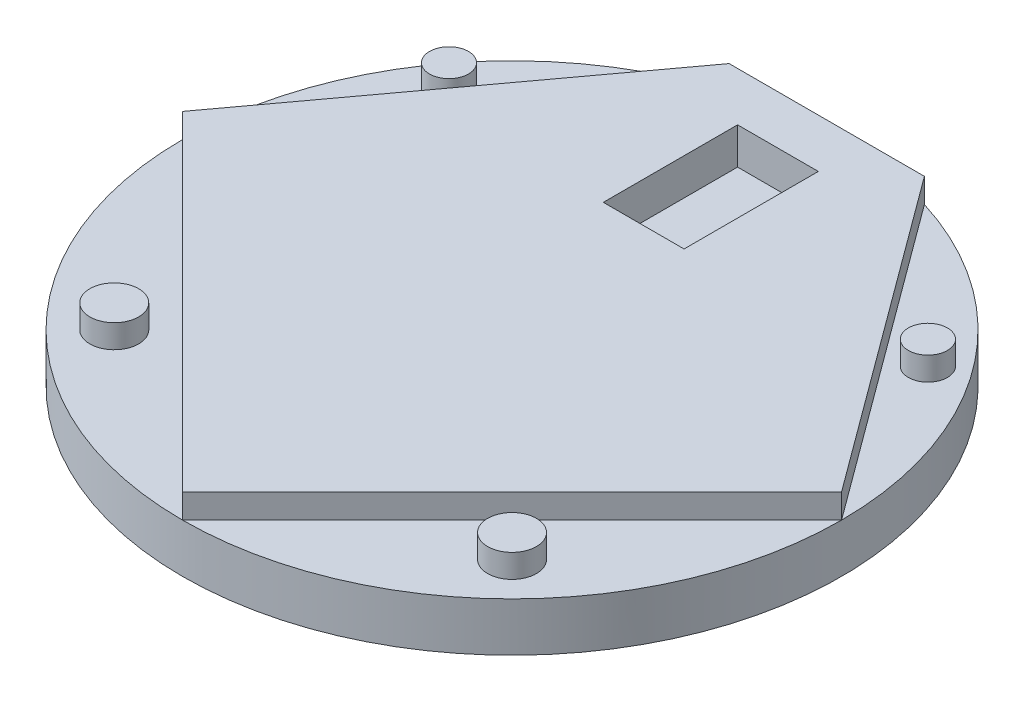
SolidWorks part; units mm, degrees
ref_plane "Front Plane" through (0, 0, 0) normal (0, 0, 1) x (1, 0, 0)
ref_plane "Top Plane" through (0, 0, 0) normal (0, 1, 0) x (1, 0, 0)
ref_plane "Right Plane" through (0, 0, 0) normal (1, 0, 0) x (0, 0, -1)
sketch "Sketch1" plane through (0, 0, 0) normal (0, 1, 0) x (1, 0, 0)
  circle A0 centre (0, 0) radius 85.725
extrude "Boss-Extrude1" add sketch "Sketch1" along normal blind 12.7
sketch "Sketch2" plane through (0, 12.7, 0) normal (0, 1, 0) x (1, 0, 0)
  line L0 (0, 0) -> (0, 85.725) construction
  line L1 (0, 0) -> (-85.725, 0) construction
  line L2 (-85.725, 0) -> (85.725, 0) construction
  line L3 (-25.4, 81.8756) -> (25.4, 81.8756)
  line L5 (-25.4, 81.8756) -> (-85.725, 0)
  line L6 (-85.725, 0) -> (0, -85.725)
  line L7 (0, -85.725) -> (85.725, 0)
  line L8 (85.725, 0) -> (25.4, 81.8756)
  circle A0 centre (0, 0) radius 85.725 construction
  dimension "D1" = 50.8
extrude "Boss-Extrude2" add sketch "Sketch2" along normal blind 6.35
sketch "Sketch3" plane through (0, 12.7, 0) normal (0, 1, 0) x (1, 0, 0)
  line L0 (-42.8625, -42.8625) -> (-60.6167, -60.6167) construction
  line L1 (-85.725, 0) -> (0, -85.725) construction
  line L2 (60.6167, -60.6167) -> (42.8625, -42.8625) construction
  line L3 (0, -85.725) -> (85.725, 0) construction
  line L4 (55.5625, 40.9378) -> (69.0152, 50.8496) construction
  line L5 (85.725, 0) -> (25.4, 81.8756) construction
  line L6 (-69.0152, 50.8496) -> (-55.5625, 40.9378) construction
  line L7 (-25.4, 81.8756) -> (-85.725, 0) construction
  circle A0 centre (-51.7396, -51.7396) radius 6.35
  arc A1 (-85.725, 0) -> (0, -85.725) centre (0, 0) ccw construction
  circle A2 centre (51.7396, -51.7396) radius 6.35
  arc A3 (0, -85.725) -> (85.725, 0) centre (0, 0) ccw construction
  circle A4 centre (62.2888, 45.8937) radius 5.08
  arc A5 (85.725, 0) -> (25.4, 81.8756) centre (0, 0) ccw construction
  arc A6 (-25.4, 81.8756) -> (-85.725, 0) centre (0, 0) ccw construction
  circle A7 centre (-62.2888, 45.8937) radius 5.08
  dimension "D1" = 12.7
  dimension "D2" = 10.16
extrude "Boss-Extrude3" add sketch "Sketch3" along normal blind 6.096
sketch "Sketch4" plane through (0, 19.05, 0) normal (0, 1, 0) x (1, 0, 0)
  line L0 (25.4, 81.8756) -> (-25.4, 81.8756) construction
  line L1 (-10.5029, 69.1756) -> (10.5029, 69.1756)
  line L2 (-10.5029, 69.1756) -> (-10.5029, 34.2506)
  line L3 (-10.5029, 34.2506) -> (10.5029, 34.2506)
  line L4 (10.5029, 69.1756) -> (10.5029, 34.2506)
  dimension "D1" = 12.7
  dimension "D2" = 21.0058
  dimension "D3" = 34.925
  dimension "D4" = 14.8971
extrude "Cut-Extrude1" cut sketch "Sketch4" against normal blind 9.525
